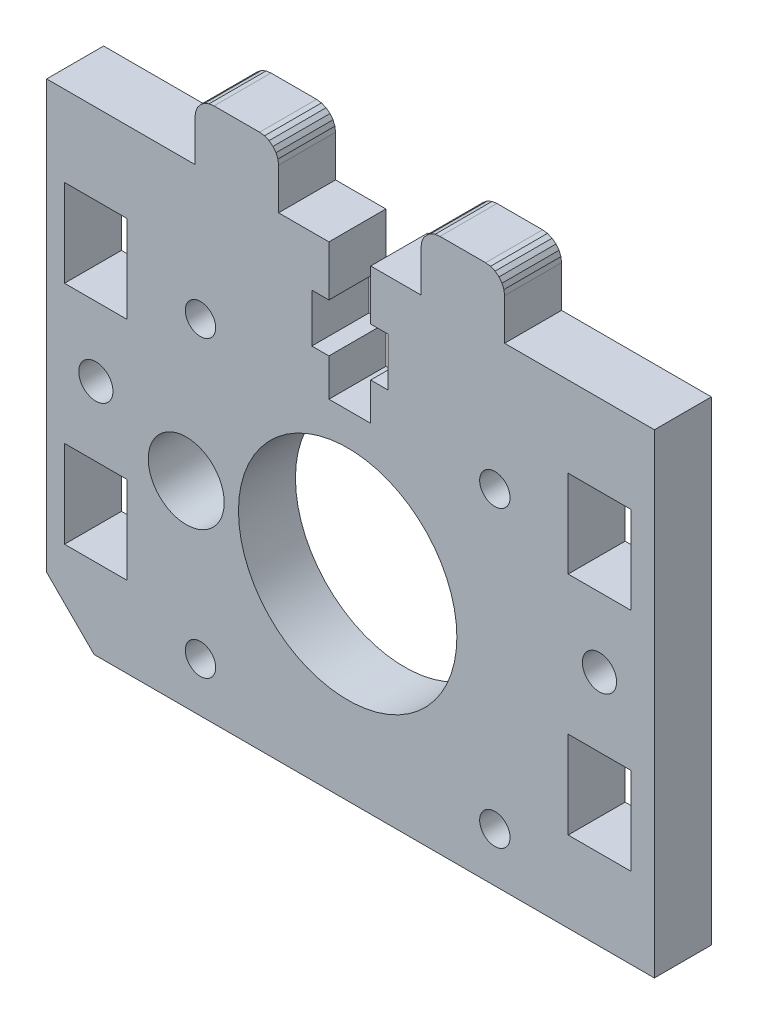
SolidWorks part; units mm, degrees
ref_plane "Plano frontal" through (0, 0, 0) normal (0, 0, 1) x (1, 0, 0)
ref_plane "Plano superior" through (0, 0, 0) normal (0, 1, 0) x (1, 0, 0)
ref_plane "Plano direito" through (0, 0, 0) normal (1, 0, 0) x (0, 0, -1)
sketch "Model" plane through (0, 0, 0) normal (0, 0, 1) x (1, 0, 0)
  line L0 (68.1605, 58.419) -> (68.1605, 53.119)
  line L1 (34.0355, 13.419) -> (39.0355, 8.419)
  line L2 (63.7605, 48.019) -> (61.9605, 48.019)
  line L3 (82.2605, 58.419) -> (82.2605, 62.769)
  line L4 (61.9605, 48.019) -> (61.9605, 53.119)
  line L5 (73.4605, 58.419) -> (68.1605, 58.419)
  line L6 (58.4605, 58.419) -> (58.4605, 62.769)
  line L7 (95.5555, 49.919) -> (95.5555, 40.719)
  line L8 (61.9605, 53.119) -> (63.7605, 53.119)
  line L9 (95.5555, 40.719) -> (88.9555, 40.719)
  line L10 (34.0355, 58.419) -> (34.0355, 13.419)
  line L11 (68.1605, 53.119) -> (69.9605, 53.119)
  line L12 (63.7605, 58.419) -> (58.4605, 58.419)
  line L13 (69.9605, 48.019) -> (68.1605, 48.019)
  line L14 (63.7605, 53.119) -> (63.7605, 58.419)
  line L15 (69.9605, 53.119) -> (69.9605, 48.019)
  line L16 (88.9555, 40.719) -> (88.9555, 49.919)
  line L17 (88.9555, 49.919) -> (95.5555, 49.919)
  line L18 (68.1605, 44.069) -> (63.7605, 44.069)
  line L19 (63.7605, 44.069) -> (63.7605, 48.019)
  line L20 (68.1605, 48.019) -> (68.1605, 44.069)
  line L21 (82.2605, 62.769) -> (82.1923, 63.2866)
  line L22 (82.1923, 63.2866) -> (81.9925, 63.769)
  line L23 (81.9925, 63.769) -> (81.6747, 64.1832)
  line L24 (81.6747, 64.1832) -> (81.2605, 64.501)
  line L25 (81.2605, 64.501) -> (80.7781, 64.7008)
  line L26 (80.2605, 64.769) -> (75.4605, 64.769)
  line L27 (80.7781, 64.7008) -> (80.2605, 64.769)
  line L28 (49.6605, 62.769) -> (49.6605, 58.419)
  line L29 (49.6605, 62.769) -> (49.7287, 63.2866)
  line L30 (49.7287, 63.2866) -> (49.9285, 63.769)
  line L31 (49.9285, 63.769) -> (50.2463, 64.1832)
  line L32 (50.2463, 64.1832) -> (50.6605, 64.501)
  line L33 (50.6605, 64.501) -> (51.1429, 64.7008)
  line L34 (51.1429, 64.7008) -> (51.6605, 64.769)
  line L35 (58.4605, 62.769) -> (58.3924, 63.2866)
  line L36 (58.3924, 63.2866) -> (58.1926, 63.769)
  line L37 (58.1926, 63.769) -> (57.8747, 64.1832)
  line L38 (57.8747, 64.1832) -> (57.4605, 64.501)
  line L39 (57.4605, 64.501) -> (56.9781, 64.7008)
  line L40 (56.4605, 64.769) -> (51.6605, 64.769)
  line L41 (56.9781, 64.7008) -> (56.4605, 64.769)
  line L42 (73.4605, 62.769) -> (73.4605, 58.419)
  line L43 (73.4605, 62.769) -> (73.5286, 63.2866)
  line L44 (73.5286, 63.2866) -> (73.7284, 63.769)
  line L45 (73.7284, 63.769) -> (74.0463, 64.1832)
  line L46 (74.0463, 64.1832) -> (74.4605, 64.501)
  line L47 (74.4605, 64.501) -> (74.9429, 64.7008)
  line L48 (74.9429, 64.7008) -> (75.4605, 64.769)
  line L49 (35.9155, 40.719) -> (35.9155, 49.919)
  line L50 (35.9155, 49.919) -> (42.5155, 49.919)
  line L51 (42.5155, 49.919) -> (42.5155, 40.719)
  line L52 (42.5155, 40.719) -> (35.9155, 40.719)
  line L53 (42.5155, 26.119) -> (42.5155, 16.919)
  line L54 (42.5155, 16.919) -> (35.9155, 16.919)
  line L55 (35.9155, 16.919) -> (35.9155, 26.119)
  line L56 (35.9155, 26.119) -> (42.5155, 26.119)
  line L57 (95.5555, 26.119) -> (95.5555, 16.919)
  line L58 (95.5555, 16.919) -> (88.9555, 16.919)
  line L59 (88.9555, 16.919) -> (88.9555, 26.119)
  line L60 (88.9555, 26.119) -> (95.5555, 26.119)
  line L61 (98.0355, 58.419) -> (82.2605, 58.419)
  line L62 (98.0355, 8.419) -> (98.0355, 58.419)
  line L63 (39.0355, 8.419) -> (98.0355, 8.419)
  line L64 (49.6605, 58.419) -> (34.0355, 58.419)
  circle A0 centre (50.2355, 44.619) radius 1.6
  circle A1 centre (50.2355, 13.619) radius 1.6
  circle A2 centre (81.2355, 13.619) radius 1.6
  circle A3 centre (81.2355, 44.619) radius 1.6
  circle A4 centre (92.2555, 33.419) radius 1.8
  circle A5 centre (39.2155, 33.419) radius 1.8
  circle A6 centre (48.7355, 29.119) radius 4
  circle A7 centre (65.7355, 29.119) radius 11.5
extrude "Ressalto-extrusão1" add sketch "Model" along normal blind 6
ref_plane "Plano1" through (0, 33.419, 0) normal (0, -1, 0) x (-1, 0, 0)
